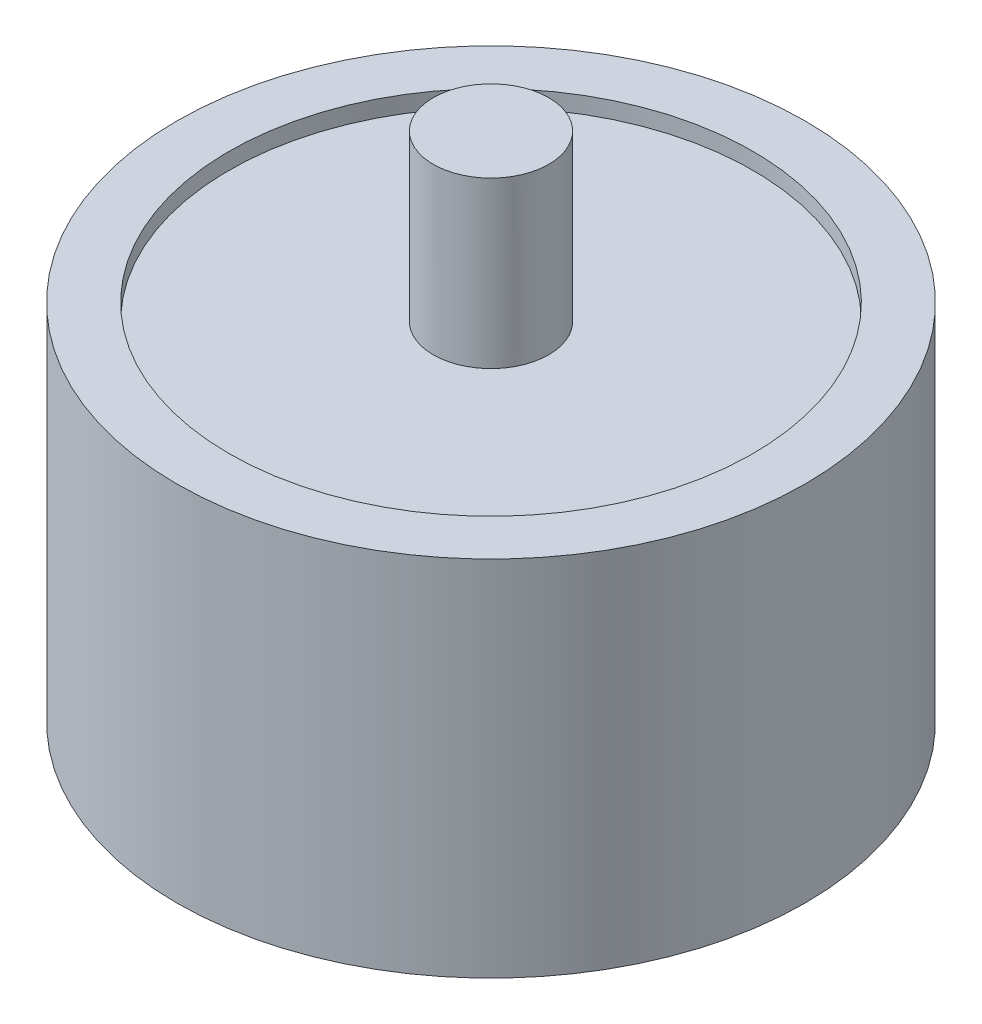
SolidWorks part; units mm, degrees
ref_plane "Front Plane" through (0, 0, 0) normal (0, 0, 1) x (1, 0, 0)
ref_plane "Top Plane" through (0, 0, 0) normal (0, 1, 0) x (1, 0, 0)
ref_plane "Right Plane" through (0, 0, 0) normal (1, 0, 0) x (0, 0, -1)
sketch "Sketch1" plane through (0, 0, 0) normal (0, 1, 0) x (1, 0, 0)
  circle A0 centre (0, 0) radius 15.875
  dimension "D1" = 31.75
extrude "Boss-Extrude1" add sketch "Sketch1" along normal blind 20
sketch "Sketch2" plane through (0, 0, 0) normal (0, -1, 0) x (1, 0, 0)
  circle A0 centre (0, 0) radius 3.5
  dimension "D1" = 7
extrude "Boss-Extrude2" add sketch "Sketch2" along normal blind 10 and the other way blind 30
sketch "Sketch3" plane through (0, 0, 0) normal (0, 1, 0) x (1, 0, 0)
  circle A0 centre (0, 0) radius 19.05
  circle A1 centre (0, 0) radius 15.875
  circle A3 centre (0, 0) radius 15.875 construction
  dimension "D1" = 38.1
extrude "Boss-Extrude3" add sketch "Sketch3" against normal blind 1 and the other way blind 21
